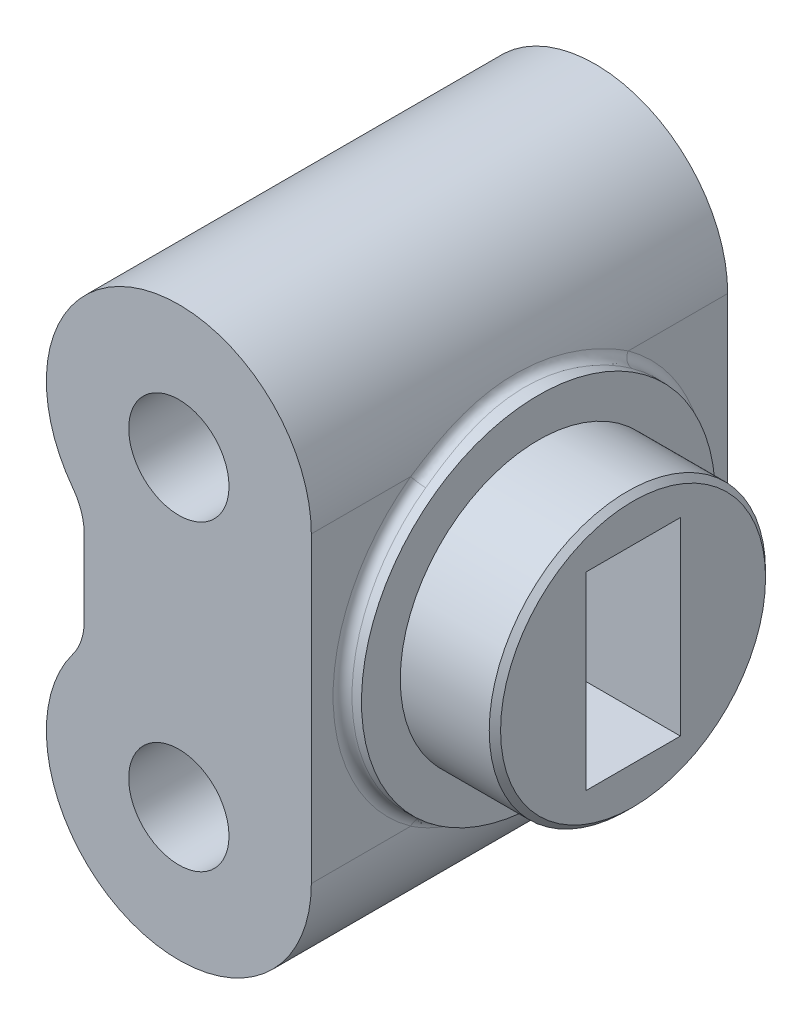
SolidWorks part; units mm, degrees
ref_plane "前视基准面" through (0, 0, 0) normal (0, 0, 1) x (1, 0, 0)
ref_plane "上视基准面" through (0, 0, 0) normal (0, 1, 0) x (1, 0, 0)
ref_plane "右视基准面" through (0, 0, 0) normal (1, 0, 0) x (0, 0, -1)
other "Configuration Table"
sketch "草图1" plane through (0, 0, 0) normal (0, 0, 1) x (1, 0, 0)
  line L0 (0, 0) -> (0, 21.6204) construction
  line L1 (0, 0) -> (-7, 0) construction
  line L2 (-7, 0) -> (-7, -16)
  line L3 (7, 0) -> (7, -16)
  circle A0 centre (0, 0) radius 2.65
  circle A1 centre (0, -16) radius 2.65
  arc A2 (7, 0) -> (-7, 0) centre (0, 0) ccw
  arc A3 (-7, -16) -> (7, -16) centre (0, -16) ccw
  dimension "D2" = 5.3
  dimension "D3" = 14
  dimension "D1" = 16
extrude "凸台-拉伸1" add sketch "草图1" along normal blind 22
sketch "草图2" plane through (0, 0, 22) normal (0, 0, 1) x (1, 0, 0)
  line L0 (0, 0) -> (0, -16) construction
  line L1 (-5, -6) -> (-5, -10)
  line L2 (-7, 0) -> (-7, -16) construction
  line L3 (-7, 0) -> (-7, -16)
  arc A0 (-7, 0) -> (-5.6, -4.2) centre (0, 0) ccw
  arc A1 (-5.6, -11.8) -> (-7, -16) centre (0, -16) ccw
  arc A2 (-5, -10) -> (-5.6, -11.8) centre (-8, -10) cw
  arc A3 (-5, -6) -> (-5.6, -4.2) centre (-8, -6) ccw
  dimension "D2" = 3
  dimension "D1" = 10
extrude "切除-拉伸1" cut sketch "草图2" against normal through all
sketch "草图3" plane through (7, 0, 0) normal (1, 0, 0) x (0, 0, -1)
  line L0 (0, -8) -> (-22, -8) construction
  line L1 (0, -16) -> (0, 0) construction
  line L2 (-22, -16) -> (-22, 0) construction
  line L3 (-11, -23) -> (-11, 7) construction
  line L4 (-22, -23) -> (0, -23) construction
  line L5 (0, 7) -> (-22, 7) construction
  circle A1 centre (-11, -8) radius 9.35
  dimension "D1" = 18.7
extrude "凸台-拉伸2" add sketch "草图3" along normal blind 1 and the other way up to body (1 mm away) separate body
sketch "草图4" plane through (8, 0, 0) normal (1, 0, 0) x (0, 0, -1)
  circle A2 centre (-11, -8) radius 7.3
  arc A3 (-6.1603, -16) -> (-6.1603, 0) centre (-11, -8) ccw construction
  dimension "D1" = 14.6
extrude "凸台-拉伸3" add sketch "草图4" along normal blind 5
chamfer "倒角1" distance 0.3 angle 45 1 edges at (13, -8, 3.7)
sketch "草图5" plane through (13, 0, 0) normal (1, 0, 0) x (0, 0, -1)
  line L1 (-13.5, -3) -> (-8.5, -3)
  line L2 (-13.5, -3) -> (-13.5, -13)
  line L3 (-13.5, -13) -> (-8.5, -13)
  line L4 (-8.5, -3) -> (-8.5, -13)
  line L5 (-13.5, -3) -> (-8.5, -13) construction
  line L6 (-13.5, -13) -> (-8.5, -3) construction
  point P0 (-11, -8)
  dimension "D1" = 5
  dimension "D2" = 10
extrude "切除-拉伸2" cut sketch "草图5" against normal up to surface (5 mm away) up to face at (8, -8, 3.7)
fillet "圆角1" radius 0.5 4 edges at (6.8911, 1.23, 9.5068) (7, -8, 20.35) (7, -8, 1.65) (-6.8686, -17.3497, 11.0708)
